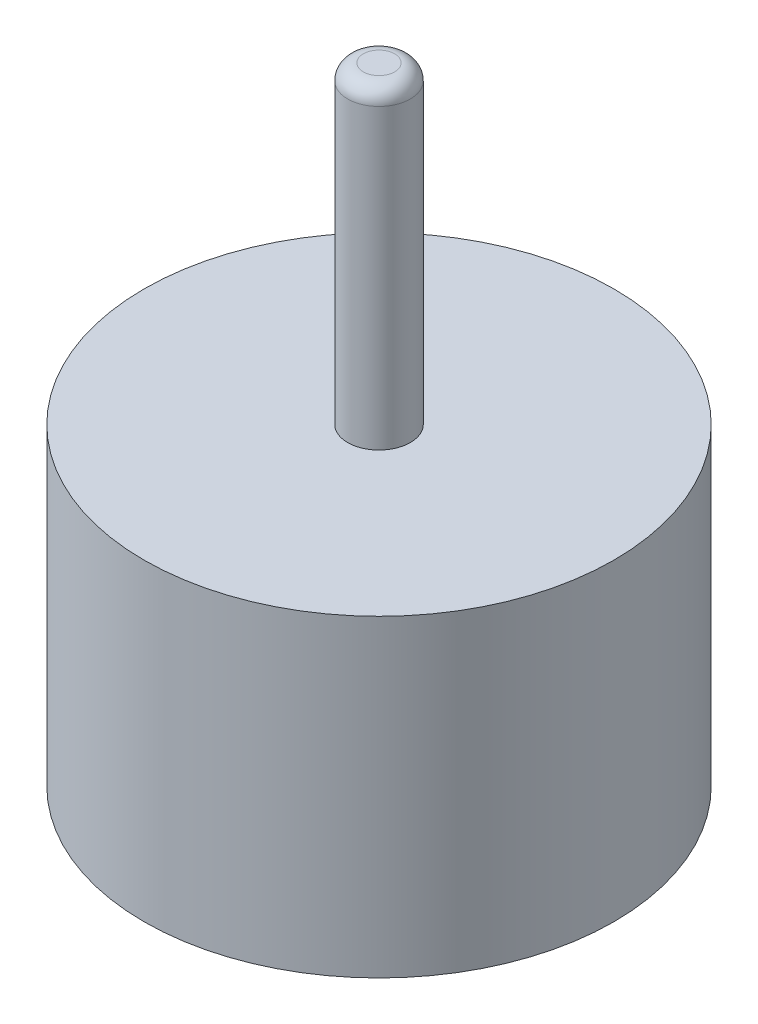
SolidWorks part; units mm, degrees
ref_plane "前视基准面" through (0, 0, 0) normal (0, 0, 1) x (1, 0, 0)
ref_plane "上视基准面" through (0, 0, 0) normal (0, 1, 0) x (1, 0, 0)
ref_plane "右视基准面" through (0, 0, 0) normal (1, 0, 0) x (0, 0, -1)
sketch "草图1" plane through (0, 0, 0) normal (0, 1, 0) x (1, 0, 0)
  circle A0 centre (0, 0) radius 75
  dimension "D1" = 150
extrude "凸台-拉伸1" add sketch "草图1" along normal blind 100
sketch "草图2" plane through (0, 100, 0) normal (0, 1, 0) x (1, 0, 0)
  circle A0 centre (0, 0) radius 10
  dimension "D1" = 20
extrude "凸台-拉伸2" add sketch "草图2" along normal blind 100
fillet "圆角1" radius 5 1 edges at (0, 200, 10)
